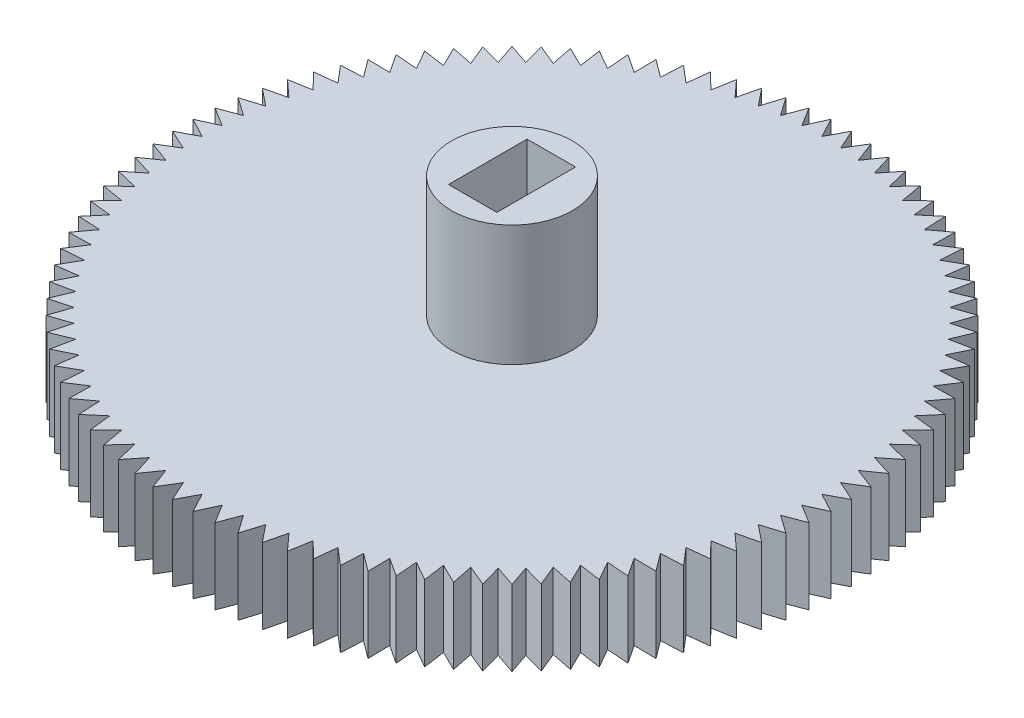
SolidWorks part; units mm, degrees
ref_plane "Front Plane" through (0, 0, 0) normal (0, 0, 1) x (1, 0, 0)
ref_plane "Top Plane" through (0, 0, 0) normal (0, 1, 0) x (1, 0, 0)
ref_plane "Right Plane" through (0, 0, 0) normal (1, 0, 0) x (0, 0, -1)
sketch "Sketch1" plane through (0, 0, 0) normal (0, 1, 0) x (1, 0, 0)
  line L0 (0, 0) -> (0, 20.5) construction
  line L1 (0, 20.5) -> (0.6848, 21.7905)
  line L2 (0.6848, 21.7905) -> (1.2872, 20.4595)
  line L3 (1.2872, 20.4595) -> (0, 0) construction
  line L4 (2.0517, 21.7045) -> (2.5693, 20.3384)
  line L5 (1.2872, 20.4595) -> (2.0517, 21.7045)
  line L6 (3.4105, 21.5328) -> (3.8413, 20.1369)
  line L7 (2.5693, 20.3384) -> (3.4105, 21.5328)
  line L8 (4.7558, 21.2762) -> (5.0981, 19.856)
  line L9 (3.8413, 20.1369) -> (4.7558, 21.2762)
  line L10 (6.0824, 20.9356) -> (6.3348, 19.4967)
  line L11 (5.0981, 19.856) -> (6.0824, 20.9356)
  line L12 (7.3849, 20.5124) -> (7.5466, 19.0604)
  line L13 (6.3348, 19.4967) -> (7.3849, 20.5124)
  line L14 (8.6583, 20.0082) -> (8.7285, 18.549)
  line L15 (7.5466, 19.0604) -> (8.6583, 20.0082)
  line L16 (9.8976, 19.4251) -> (9.876, 17.9643)
  line L17 (8.7285, 18.549) -> (9.8976, 19.4251)
  line L18 (11.0977, 18.7653) -> (10.9844, 17.3087)
  line L19 (9.876, 17.9643) -> (11.0977, 18.7653)
  line L20 (12.2541, 18.0314) -> (12.0496, 16.5848)
  line L21 (10.9844, 17.3087) -> (12.2541, 18.0314)
  line L22 (13.3621, 17.2264) -> (13.0672, 15.7955)
  line L23 (12.0496, 16.5848) -> (13.3621, 17.2264)
  line L24 (14.4174, 16.3534) -> (14.0332, 14.9439)
  line L25 (13.0672, 15.7955) -> (14.4174, 16.3534)
  line L26 (15.4158, 15.4158) -> (14.9439, 14.0332)
  line L27 (14.0332, 14.9439) -> (15.4158, 15.4158)
  line L28 (16.3534, 14.4174) -> (15.7955, 13.0672)
  line L29 (14.9439, 14.0332) -> (16.3534, 14.4174)
  line L30 (17.2264, 13.3621) -> (16.5848, 12.0496)
  line L31 (15.7955, 13.0672) -> (17.2264, 13.3621)
  line L32 (18.0314, 12.2541) -> (17.3087, 10.9844)
  line L33 (16.5848, 12.0496) -> (18.0314, 12.2541)
  line L34 (18.7653, 11.0977) -> (17.9643, 9.876)
  line L35 (17.3087, 10.9844) -> (18.7653, 11.0977)
  line L36 (19.4251, 9.8976) -> (18.549, 8.7285)
  line L37 (17.9643, 9.876) -> (19.4251, 9.8976)
  line L38 (20.0082, 8.6583) -> (19.0604, 7.5466)
  line L39 (18.549, 8.7285) -> (20.0082, 8.6583)
  line L40 (20.5124, 7.3849) -> (19.4967, 6.3348)
  line L41 (19.0604, 7.5466) -> (20.5124, 7.3849)
  line L42 (20.9356, 6.0824) -> (19.856, 5.0981)
  line L43 (19.4967, 6.3348) -> (20.9356, 6.0824)
  line L44 (21.2762, 4.7558) -> (20.1369, 3.8413)
  line L45 (19.856, 5.0981) -> (21.2762, 4.7558)
  line L46 (21.5328, 3.4105) -> (20.3384, 2.5693)
  line L47 (20.1369, 3.8413) -> (21.5328, 3.4105)
  line L48 (21.7045, 2.0517) -> (20.4595, 1.2872)
  line L49 (20.3384, 2.5693) -> (21.7045, 2.0517)
  line L50 (21.7905, 0.6848) -> (20.5, 0)
  line L51 (20.4595, 1.2872) -> (21.7905, 0.6848)
  line L52 (21.7905, -0.6848) -> (20.4595, -1.2872)
  line L53 (20.5, 0) -> (21.7905, -0.6848)
  line L54 (21.7045, -2.0517) -> (20.3384, -2.5693)
  line L55 (20.4595, -1.2872) -> (21.7045, -2.0517)
  line L56 (21.5328, -3.4105) -> (20.1369, -3.8413)
  line L57 (20.3384, -2.5693) -> (21.5328, -3.4105)
  line L58 (21.2762, -4.7558) -> (19.856, -5.0981)
  line L59 (20.1369, -3.8413) -> (21.2762, -4.7558)
  line L60 (20.9356, -6.0824) -> (19.4967, -6.3348)
  line L61 (19.856, -5.0981) -> (20.9356, -6.0824)
  line L62 (20.5124, -7.3849) -> (19.0604, -7.5466)
  line L63 (19.4967, -6.3348) -> (20.5124, -7.3849)
  line L64 (20.0082, -8.6583) -> (18.549, -8.7285)
  line L65 (19.0604, -7.5466) -> (20.0082, -8.6583)
  line L66 (19.4251, -9.8976) -> (17.9643, -9.876)
  line L67 (18.549, -8.7285) -> (19.4251, -9.8976)
  line L68 (18.7653, -11.0977) -> (17.3087, -10.9844)
  line L69 (17.9643, -9.876) -> (18.7653, -11.0977)
  line L70 (18.0314, -12.2541) -> (16.5848, -12.0496)
  line L71 (17.3087, -10.9844) -> (18.0314, -12.2541)
  line L72 (17.2264, -13.3621) -> (15.7955, -13.0672)
  line L73 (16.5848, -12.0496) -> (17.2264, -13.3621)
  line L74 (16.3534, -14.4174) -> (14.9439, -14.0332)
  line L75 (15.7955, -13.0672) -> (16.3534, -14.4174)
  line L76 (15.4158, -15.4158) -> (14.0332, -14.9439)
  line L77 (14.9439, -14.0332) -> (15.4158, -15.4158)
  line L78 (14.4174, -16.3534) -> (13.0672, -15.7955)
  line L79 (14.0332, -14.9439) -> (14.4174, -16.3534)
  line L80 (13.3621, -17.2264) -> (12.0496, -16.5848)
  line L81 (13.0672, -15.7955) -> (13.3621, -17.2264)
  line L82 (12.2541, -18.0314) -> (10.9844, -17.3087)
  line L83 (12.0496, -16.5848) -> (12.2541, -18.0314)
  line L84 (11.0977, -18.7653) -> (9.876, -17.9643)
  line L85 (10.9844, -17.3087) -> (11.0977, -18.7653)
  line L86 (9.8976, -19.4251) -> (8.7285, -18.549)
  line L87 (9.876, -17.9643) -> (9.8976, -19.4251)
  line L88 (8.6583, -20.0082) -> (7.5466, -19.0604)
  line L89 (8.7285, -18.549) -> (8.6583, -20.0082)
  line L90 (7.3849, -20.5124) -> (6.3348, -19.4967)
  line L91 (7.5466, -19.0604) -> (7.3849, -20.5124)
  line L92 (6.0824, -20.9356) -> (5.0981, -19.856)
  line L93 (6.3348, -19.4967) -> (6.0824, -20.9356)
  line L94 (4.7558, -21.2762) -> (3.8413, -20.1369)
  line L95 (5.0981, -19.856) -> (4.7558, -21.2762)
  line L96 (3.4105, -21.5328) -> (2.5693, -20.3384)
  line L97 (3.8413, -20.1369) -> (3.4105, -21.5328)
  line L98 (2.0517, -21.7045) -> (1.2872, -20.4595)
  line L99 (2.5693, -20.3384) -> (2.0517, -21.7045)
  line L100 (0.6848, -21.7905) -> (0, -20.5)
  line L101 (1.2872, -20.4595) -> (0.6848, -21.7905)
  line L102 (-0.6848, -21.7905) -> (-1.2872, -20.4595)
  line L103 (0, -20.5) -> (-0.6848, -21.7905)
  line L104 (-2.0517, -21.7045) -> (-2.5693, -20.3384)
  line L105 (-1.2872, -20.4595) -> (-2.0517, -21.7045)
  line L106 (-3.4105, -21.5328) -> (-3.8413, -20.1369)
  line L107 (-2.5693, -20.3384) -> (-3.4105, -21.5328)
  line L108 (-4.7558, -21.2762) -> (-5.0981, -19.856)
  line L109 (-3.8413, -20.1369) -> (-4.7558, -21.2762)
  line L110 (-6.0824, -20.9356) -> (-6.3348, -19.4967)
  line L111 (-5.0981, -19.856) -> (-6.0824, -20.9356)
  line L112 (-7.3849, -20.5124) -> (-7.5466, -19.0604)
  line L113 (-6.3348, -19.4967) -> (-7.3849, -20.5124)
  line L114 (-8.6583, -20.0082) -> (-8.7285, -18.549)
  line L115 (-7.5466, -19.0604) -> (-8.6583, -20.0082)
  line L116 (-9.8976, -19.4251) -> (-9.876, -17.9643)
  line L117 (-8.7285, -18.549) -> (-9.8976, -19.4251)
  line L118 (-11.0977, -18.7653) -> (-10.9844, -17.3087)
  line L119 (-9.876, -17.9643) -> (-11.0977, -18.7653)
  line L120 (-12.2541, -18.0314) -> (-12.0496, -16.5848)
  line L121 (-10.9844, -17.3087) -> (-12.2541, -18.0314)
  line L122 (-13.3621, -17.2264) -> (-13.0672, -15.7955)
  line L123 (-12.0496, -16.5848) -> (-13.3621, -17.2264)
  line L124 (-14.4174, -16.3534) -> (-14.0332, -14.9439)
  line L125 (-13.0672, -15.7955) -> (-14.4174, -16.3534)
  line L126 (-15.4158, -15.4158) -> (-14.9439, -14.0332)
  line L127 (-14.0332, -14.9439) -> (-15.4158, -15.4158)
  line L128 (-16.3534, -14.4174) -> (-15.7955, -13.0672)
  line L129 (-14.9439, -14.0332) -> (-16.3534, -14.4174)
  line L130 (-17.2264, -13.3621) -> (-16.5848, -12.0496)
  line L131 (-15.7955, -13.0672) -> (-17.2264, -13.3621)
  line L132 (-18.0314, -12.2541) -> (-17.3087, -10.9844)
  line L133 (-16.5848, -12.0496) -> (-18.0314, -12.2541)
  line L134 (-18.7653, -11.0977) -> (-17.9643, -9.876)
  line L135 (-17.3087, -10.9844) -> (-18.7653, -11.0977)
  line L136 (-19.4251, -9.8976) -> (-18.549, -8.7285)
  line L137 (-17.9643, -9.876) -> (-19.4251, -9.8976)
  line L138 (-20.0082, -8.6583) -> (-19.0604, -7.5466)
  line L139 (-18.549, -8.7285) -> (-20.0082, -8.6583)
  line L140 (-20.5124, -7.3849) -> (-19.4967, -6.3348)
  line L141 (-19.0604, -7.5466) -> (-20.5124, -7.3849)
  line L142 (-20.9356, -6.0824) -> (-19.856, -5.0981)
  line L143 (-19.4967, -6.3348) -> (-20.9356, -6.0824)
  line L144 (-21.2762, -4.7558) -> (-20.1369, -3.8413)
  line L145 (-19.856, -5.0981) -> (-21.2762, -4.7558)
  line L146 (-21.5328, -3.4105) -> (-20.3384, -2.5693)
  line L147 (-20.1369, -3.8413) -> (-21.5328, -3.4105)
  line L148 (-21.7045, -2.0517) -> (-20.4595, -1.2872)
  line L149 (-20.3384, -2.5693) -> (-21.7045, -2.0517)
  line L150 (-21.7905, -0.6848) -> (-20.5, 0)
  line L151 (-20.4595, -1.2872) -> (-21.7905, -0.6848)
  line L152 (-21.7905, 0.6848) -> (-20.4595, 1.2872)
  line L153 (-20.5, 0) -> (-21.7905, 0.6848)
  line L154 (-21.7045, 2.0517) -> (-20.3384, 2.5693)
  line L155 (-20.4595, 1.2872) -> (-21.7045, 2.0517)
  line L156 (-21.5328, 3.4105) -> (-20.1369, 3.8413)
  line L157 (-20.3384, 2.5693) -> (-21.5328, 3.4105)
  line L158 (-21.2762, 4.7558) -> (-19.856, 5.0981)
  line L159 (-20.1369, 3.8413) -> (-21.2762, 4.7558)
  line L160 (-20.9356, 6.0824) -> (-19.4967, 6.3348)
  line L161 (-19.856, 5.0981) -> (-20.9356, 6.0824)
  line L162 (-20.5124, 7.3849) -> (-19.0604, 7.5466)
  line L163 (-19.4967, 6.3348) -> (-20.5124, 7.3849)
  line L164 (-20.0082, 8.6583) -> (-18.549, 8.7285)
  line L165 (-19.0604, 7.5466) -> (-20.0082, 8.6583)
  line L166 (-19.4251, 9.8976) -> (-17.9643, 9.876)
  line L167 (-18.549, 8.7285) -> (-19.4251, 9.8976)
  line L168 (-18.7653, 11.0977) -> (-17.3087, 10.9844)
  line L169 (-17.9643, 9.876) -> (-18.7653, 11.0977)
  line L170 (-18.0314, 12.2541) -> (-16.5848, 12.0496)
  line L171 (-17.3087, 10.9844) -> (-18.0314, 12.2541)
  line L172 (-17.2264, 13.3621) -> (-15.7955, 13.0672)
  line L173 (-16.5848, 12.0496) -> (-17.2264, 13.3621)
  line L174 (-16.3534, 14.4174) -> (-14.9439, 14.0332)
  line L175 (-15.7955, 13.0672) -> (-16.3534, 14.4174)
  line L176 (-15.4158, 15.4158) -> (-14.0332, 14.9439)
  line L177 (-14.9439, 14.0332) -> (-15.4158, 15.4158)
  line L178 (-14.4174, 16.3534) -> (-13.0672, 15.7955)
  line L179 (-14.0332, 14.9439) -> (-14.4174, 16.3534)
  line L180 (-13.3621, 17.2264) -> (-12.0496, 16.5848)
  line L181 (-13.0672, 15.7955) -> (-13.3621, 17.2264)
  line L182 (-12.2541, 18.0314) -> (-10.9844, 17.3087)
  line L183 (-12.0496, 16.5848) -> (-12.2541, 18.0314)
  line L184 (-11.0977, 18.7653) -> (-9.876, 17.9643)
  line L185 (-10.9844, 17.3087) -> (-11.0977, 18.7653)
  line L186 (-9.8976, 19.4251) -> (-8.7285, 18.549)
  line L187 (-9.876, 17.9643) -> (-9.8976, 19.4251)
  line L188 (-8.6583, 20.0082) -> (-7.5466, 19.0604)
  line L189 (-8.7285, 18.549) -> (-8.6583, 20.0082)
  line L190 (-7.3849, 20.5124) -> (-6.3348, 19.4967)
  line L191 (-7.5466, 19.0604) -> (-7.3849, 20.5124)
  line L192 (-6.0824, 20.9356) -> (-5.0981, 19.856)
  line L193 (-6.3348, 19.4967) -> (-6.0824, 20.9356)
  line L194 (-4.7558, 21.2762) -> (-3.8413, 20.1369)
  line L195 (-5.0981, 19.856) -> (-4.7558, 21.2762)
  line L196 (-3.4105, 21.5328) -> (-2.5693, 20.3384)
  line L197 (-3.8413, 20.1369) -> (-3.4105, 21.5328)
  line L198 (-2.0517, 21.7045) -> (-1.2872, 20.4595)
  line L199 (-2.5693, 20.3384) -> (-2.0517, 21.7045)
  line L200 (-0.6848, 21.7905) -> (0, 20.5)
  line L201 (-1.2872, 20.4595) -> (-0.6848, 21.7905)
  circle A0 centre (0, 0) radius 20.5 construction
  point P306 (0, 0)
  dimension "D1" = 41
  dimension "D2" = 3.6
  dimension "D3" = 21.7905
  dimension "D4" = 100
extrude "Boss-Extrude1" add sketch "Sketch1" along normal blind 5 contours L201 L198 L199 L196 L197 L194 L195 L192 L193 L190 L191 L188 L189 L186 L187 L184 L185 L182 L183 L180 L181 L178 L179 L176 L177 L174 L175 L172 L173 L170 L171 L168 L169 L166 L167 L164 L165 L162 L163 L160 L161 L158 L159 L156 L157 L154 L155 L152 L153 L150 L151
sketch "Sketch2" plane through (0, 5, 0) normal (0, 1, 0) x (1, 0, 0)
  circle A0 centre (0, 0) radius 4
  dimension "D1" = 8
extrude "Boss-Extrude2" add sketch "Sketch2" along normal blind 8
sketch "Sketch3" plane through (0, 13, 0) normal (0, 1, 0) x (1, 0, 0)
  line L1 (1.6, 2.6) -> (-1.6, 2.6)
  line L2 (1.6, 2.6) -> (1.6, -2.6)
  line L3 (1.6, -2.6) -> (-1.6, -2.6)
  line L4 (-1.6, 2.6) -> (-1.6, -2.6)
  line L5 (0, -2.6) -> (0, 2.6) construction
  line L6 (1.6, 0) -> (-1.6, 0) construction
  point P0 (0, 0)
  dimension "D1" = 3.2
  dimension "D2" = 5.2
extrude "Cut-Extrude2" cut sketch "Sketch3" against normal through all
